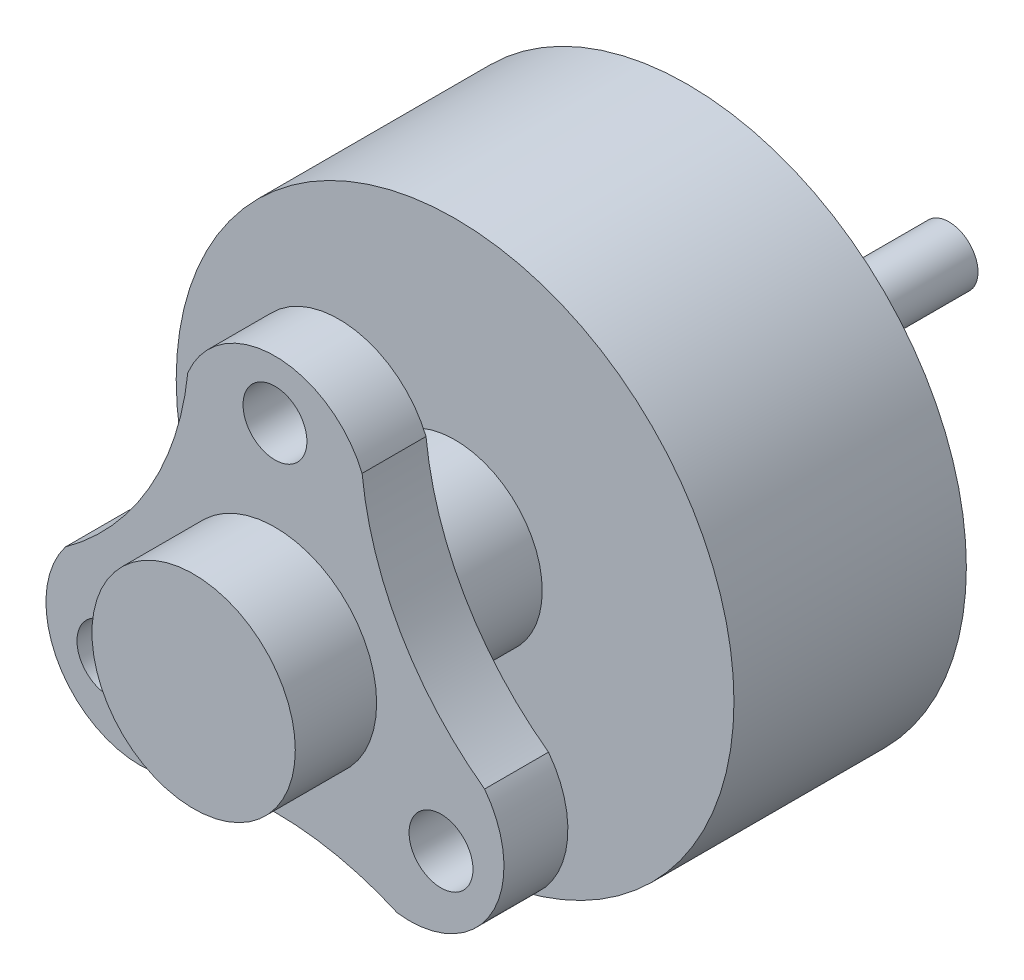
SolidWorks part; units mm, degrees
ref_plane "Front Plane" through (0, 0, 0) normal (0, 0, 1) x (1, 0, 0)
ref_plane "Top Plane" through (0, 0, 0) normal (0, 1, 0) x (1, 0, 0)
ref_plane "Right Plane" through (0, 0, 0) normal (1, 0, 0) x (0, 0, -1)
sketch "Sketch1" plane through (0, 0, 0) normal (0, 0, 1) x (1, 0, 0)
  circle A0 centre (0, 0) radius 4.8
  dimension "D1" = 9.6
extrude "Boss-Extrude1" add sketch "Sketch1" along normal blind 4
sketch "Sketch3" plane through (0, 0, 4) normal (0, 0, 1) x (1, 0, 0)
  circle A0 centre (0, 0) radius 1.5
  dimension "D1" = 3
extrude "Boss-Extrude2" add sketch "Sketch3" along normal blind 2
sketch "Sketch4" plane through (0, 0, 6) normal (0, 0, 1) x (1, 0, 0)
  line L0 (0, 0) -> (0, 3.3)
  line L1 (0, 0) -> (-2.8579, -1.65)
  line L2 (0, 0) -> (2.8579, -1.65)
  line L3 (2.1079, -2.949) -> (3.6079, -0.351)
  line L4 (-3.6079, -0.351) -> (-2.1079, -2.949)
  line L5 (0, 0) -> (-1.299, 0.75)
  line L6 (0, 0) -> (1.299, 0.75)
  line L7 (0, 0) -> (0, -1.5)
  line L8 (1.5, 3.3) -> (-1.5, 3.3)
  line L9 (0, 3.3) -> (0, 4.3)
  line L10 (2.8579, -1.65) -> (3.7239, -2.15)
  line L11 (-2.8579, -1.65) -> (-3.7239, -2.15)
  arc A0 (-2.1079, -2.949) -> (2.1079, -2.949) centre (0, -7.672) cw
  circle A1 centre (0, 0) radius 1.5 construction
  arc A2 (-3.6079, -0.351) -> (-2.1079, -2.949) centre (-2.3166, -1.3375) ccw
  arc A3 (3.6079, -0.351) -> (2.1079, -2.949) centre (2.3166, -1.3375) cw
  arc A4 (-1.5, 3.3) -> (1.5, 3.3) centre (0, 2.675) cw
  arc A5 (-1.5, 3.3) -> (-3.6079, -0.351) centre (-6.6441, 3.836) cw
  arc A6 (1.5, 3.3) -> (3.6079, -0.351) centre (6.6441, 3.836) ccw
  circle A7 centre (0, 0) radius 2.5
  point P10 (0, 3.3)
  point P11 (2.8579, -1.65)
  point P16 (-2.8579, -1.65)
  circle M7 centre (0, 0) radius 1.5
  dimension "D12" = 5
  dimension "D1" = 3.3
  dimension "D2" = 120
  dimension "D3" = 120
  dimension "D4" = 3.3
  dimension "D5" = 3.3
  dimension "D6" = 3
  dimension "D7" = 3
  dimension "D8" = 3
  dimension "D9" = 1
  dimension "D10" = 1
  dimension "D11" = 1
  dimension "D15" = 60
  dimension "D16" = 60
extrude "Boss-Extrude3" add sketch "Sketch4" along normal blind 1.1 contours A7 A6 L8 L0 | A4 L8 L9 | A4 L9 L8 | A7 L0 L8 A5 | L0 A7 L1 M7 | A7 L0 L2 M7 | L6 L2 M7 | L0 L6 M7 | L5 L0 M7 | L1 L5 M7 | L7 L1 M7 | L2 L7 M7 | L1 A7 L2 M7 | A7 L2 L3 A6 | A7 A0 L3 L2 | A7 L1 L4 A0 | A7 A5 L4 L1 | L4 A2 L11 | L11 A2 L4 | A3 L3 L10 | A3 L10 L3
hole_wizard "M1.4x0.3 Tapped Hole2" positions "Sketch12" profile "Sketch13" tap size "M1.4x0.3" standard "ANSI Metric" end condition up to next
sketch "Sketch12" plane through (0, 0, 7.1) normal (0, 0, 1) x (1, 0, 0)
  point P0 (2.8579, -1.65)
  point P2 (-2.8579, -1.65)
  point P4 (0, 3.3)
sketch "Sketch13" plane through (2.8579, -1.65, 7.1) normal (1, 0, 0) x (0, -1, 0)
  line L0 (0, 0) -> (0, 1.1)
  line L1 (0, 1.1) -> (0.55, 1.1)
  line L2 (0.55, 1.1) -> (0.55, 0)
  line L5 (0.55, 0) -> (0, 0)
  line L11 (0, -6.35) -> (0, 107.95) construction
  dimension "Thru Tap Drill Dia." = 1.1
  dimension "Thru Tap Drill Depth" = 1.1
sketch "Sketch14" plane through (0, 0, 0) normal (0, 0, -1) x (-1, 0, 0)
  circle A0 centre (0, 0) radius 0.5
  dimension "D1" = 1
extrude "Boss-Extrude4" add sketch "Sketch14" along normal blind 4.5
sketch "Sketch15" plane through (0, 0, 7.1) normal (0, 0, 1) x (1, 0, 0)
  circle A0 centre (0, 0) radius 1.75
  dimension "D1" = 3.5
extrude "Boss-Extrude5" add sketch "Sketch15" along normal blind 1.4
